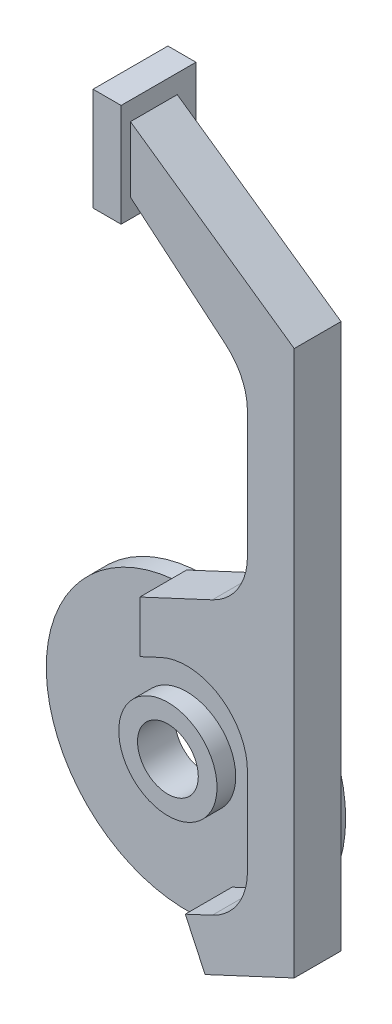
SolidWorks part; units mm, degrees
material "1060 Alloy"
ref_plane "Front Plane" through (0, 0, 0) normal (1, 0, 0) x (0, 1, 0)
ref_plane "Top Plane" through (0, 0, 0) normal (0, 0, 1) x (0, 1, 0)
ref_plane "Right Plane" through (0, 0, 0) normal (0, 1, 0) x (-1, 0, 0)
sketch "Sketch1" plane through (0, 0, 0) normal (0, 0, 1) x (0, 1, 0)
  circle A0 centre (0, 0) radius 30
  dimension "D1" = 60
extrude "Boss-Extrude1" add sketch "Sketch1" along normal blind 4
sketch "Sketch2" plane through (0, 0, 4) normal (0, 0, 1) x (1, 0, 0)
  line L0 (9.7202, -20.8451) -> (13.9464, -29.9082)
  line L1 (13.9464, -29.9082) -> (33, -21.0233)
  line L2 (33, -21.0233) -> (33, 95.4927)
  line L3 (33, 95.4927) -> (-2, 120)
  line L9 (-2, 106) -> (18.3562, 88.9191)
  line L10 (23, 78.9605) -> (23, 52.007)
  line L11 (15.494, 40.225) -> (0, 33)
  line L12 (0, 33) -> (0, 21.9662)
  line L13 (0, 21.9662) -> (4.506, 24.0674)
  line L14 (23, 12.2854) -> (23, -6.3707)
  line L15 (15.494, -18.1527) -> (9.7202, -20.8451)
  line L16 (0, 0) -> (0, -58.3484) construction
  line L17 (0, 0) -> (0, 51.6026) construction
  line L18 (-29.6224, 124) -> (23, 124) construction
  line L19 (-2, 120) -> (-2, 106)
  arc A0 (4.506, 24.0674) -> (23, 12.2854) centre (10, 12.2854) cw
  arc A1 (23, -6.3707) -> (15.494, -18.1527) centre (10, -6.3707) cw
  arc A2 (23, 52.007) -> (15.494, 40.225) centre (10, 52.007) cw
  arc A3 (18.3562, 88.9191) -> (23, 78.9605) centre (10, 78.9605) cw
  dimension "D9" = 13
  dimension "D11" = 13
  dimension "D18" = 13
  dimension "D15" = 5
  dimension "D1" = 25
  dimension "D2" = 90
  dimension "D3" = 33
  dimension "D4" = 33
  dimension "D5" = 65
  dimension "D6" = 10
  dimension "D7" = 10
  dimension "D8" = 10
  dimension "D10" = 33
  dimension "D12" = 2
  dimension "D13" = 124
  dimension "D14" = 35
  dimension "D16" = 4
  dimension "D17" = 14
extrude "Boss-Extrude2" add sketch "Sketch2" along normal blind 10
sketch "Sketch3" plane through (-2, 0, 0) normal (-1, 0, 0) x (0, -1, 0)
  line L0 (-120, 14) -> (-106, 14) construction
  line L1 (-124, 16) -> (-102, 16)
  line L2 (-124, 16) -> (-124, 0)
  line L3 (-124, 0) -> (-102, 0)
  line L4 (-102, 16) -> (-102, 0)
  line L5 (-124, 16) -> (-102, 0) construction
  line L6 (-124, 0) -> (-102, 16) construction
  line L7 (-120, 4) -> (-106, 4) construction
  line L9 (-106, 14) -> (-106, 4) construction
  line L10 (-120, 14) -> (-120, 4) construction
  point P0 (-113, 8)
  dimension "D1" = 2
  dimension "D2" = 4
  dimension "D3" = 4
  dimension "D4" = 4
extrude "Boss-Extrude3" add sketch "Sketch3" along normal blind 6
sketch "Sketch5" plane through (0, 0, 4) normal (0, 0, 1) x (1, 0, 0)
  circle A0 centre (0, 0) radius 10.5
  dimension "D1" = 21
extrude "Boss-Extrude4" add sketch "Sketch5" along normal blind 4
sketch "Sketch7" plane through (0, 0, 8) normal (0, 0, 1) x (1, 0, 0)
  circle A0 centre (0, 0) radius 6.5
  dimension "D1" = 13
extrude "Cut-Extrude3" cut sketch "Sketch7" against normal through all both and the other way through all
